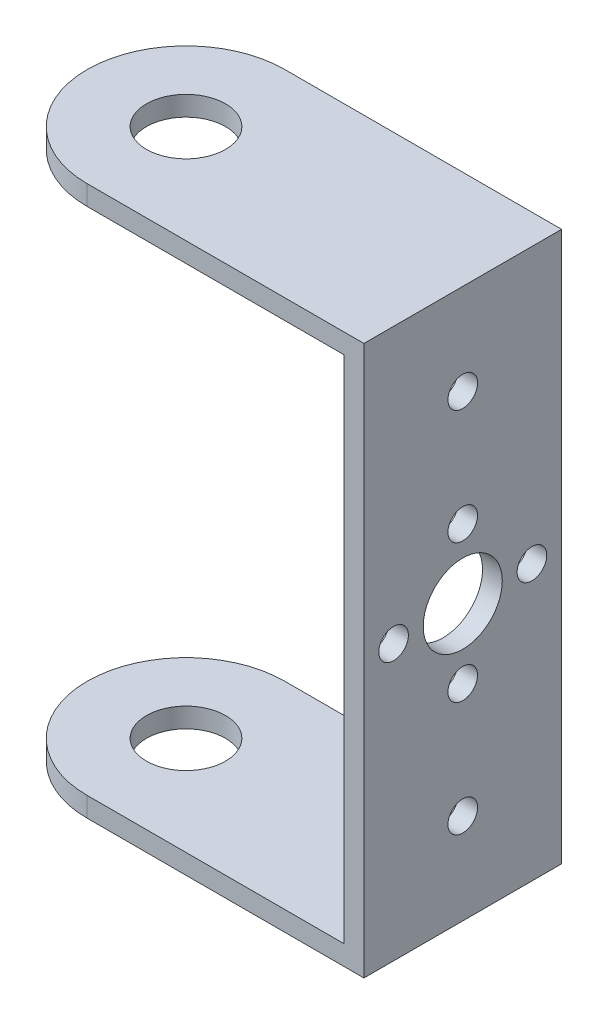
SolidWorks part; units mm, degrees
ref_plane "Alzado" through (0, 0, 0) normal (0, 0, 1) x (1, 0, 0)
ref_plane "Planta" through (0, 0, 0) normal (0, 1, 0) x (1, 0, 0)
ref_plane "Vista lateral" through (0, 0, 0) normal (1, 0, 0) x (0, 0, -1)
sketch "Croquis1" plane through (0, 0, 0) normal (0, 0, 1) x (1, 0, 0)
  line L0 (-12, 25.8) -> (12, 25.8)
  line L1 (-14, -27.8) -> (14, -27.8)
  line L3 (-14, 27.8) -> (14, 27.8)
  line L4 (14, -27.8) -> (14, 27.8)
  line L5 (-12, 25.8) -> (-14, 25.8)
  line L6 (-14, 25.8) -> (-14, 27.8)
  line L7 (12, -25.8) -> (12, 25.8)
  line L8 (-12, -25.8) -> (12, -25.8)
  line L10 (-14, -27.8) -> (-14, 27.8) construction
  line L11 (-14, -27.8) -> (-14, -25.8)
  line L12 (-14, -25.8) -> (-12, -25.8)
  line L13 (-12, -25.8) -> (-12, 25.8) construction
extrude "Saliente-Extruir1" add sketch "Croquis1" along normal blind 20
sketch "Croquis2" plane through (0, 27.8, 0) normal (0, 1, 0) x (1, 0, 0)
  line L0 (-14, -20) -> (-14, 0) construction
  line L1 (-14, -20) -> (-14, 0)
  arc A0 (-14, 0) -> (-14, -20) centre (-14, -10) ccw
extrude "Saliente-Extruir2" add sketch "Croquis2" against normal blind 2
sketch "Croquis3" plane through (0, -25.8, 0) normal (0, 1, 0) x (1, 0, 0)
  line L0 (-14, -20) -> (-14, 0) construction
  line L1 (-14, -20) -> (-14, 0)
  arc A0 (-14, 0) -> (-14, -20) centre (-14, -10) ccw
extrude "Saliente-Extruir3" add sketch "Croquis3" against normal blind 2
sketch "Croquis4" plane through (0, 27.8, 0) normal (0, 1, 0) x (1, 0, 0)
  line L0 (-14, -10) -> (-14, -20)
  circle A0 centre (-14, -10) radius 4
extrude "Cortar-Extruir1" cut sketch "Croquis4" against normal blind 2
sketch "Croquis5" plane through (0, -25.8, 0) normal (0, 1, 0) x (1, 0, 0)
  circle A0 centre (-14, -10) radius 4
extrude "Cortar-Extruir2" cut sketch "Croquis5" against normal blind 2
sketch "Croquis6" plane through (14, 0, 0) normal (1, 0, 0) x (0, 0, -1)
  line L0 (-20, 27.8) -> (0, -27.8)
  circle A0 centre (-10, 0) radius 4
extrude "Cortar-Extruir3" cut sketch "Croquis6" against normal blind 2 contours L0 A0 | L0 A0
sketch "Croquis7" plane through (14, 0, 0) normal (1, 0, 0) x (0, 0, -1)
  circle A1 centre (-10, 7) radius 1.5
  circle A3 centre (-3, 0) radius 1.5
  circle A4 centre (-10, -7) radius 1.5
  circle A5 centre (-17, 0) radius 1.5
  point P14 (-10, 0)
  dimension "D1" = 4
extrude "Cortar-Extruir4" cut sketch "Croquis7" against normal blind 2
sketch "Croquis8" plane through (14, 0, 0) normal (1, 0, 0) x (0, 0, -1)
  circle A1 centre (-10, 18.6) radius 1.5
  circle A2 centre (-10, -18.6) radius 1.5
extrude "Cortar-Extruir5" cut sketch "Croquis8" against normal blind 2
